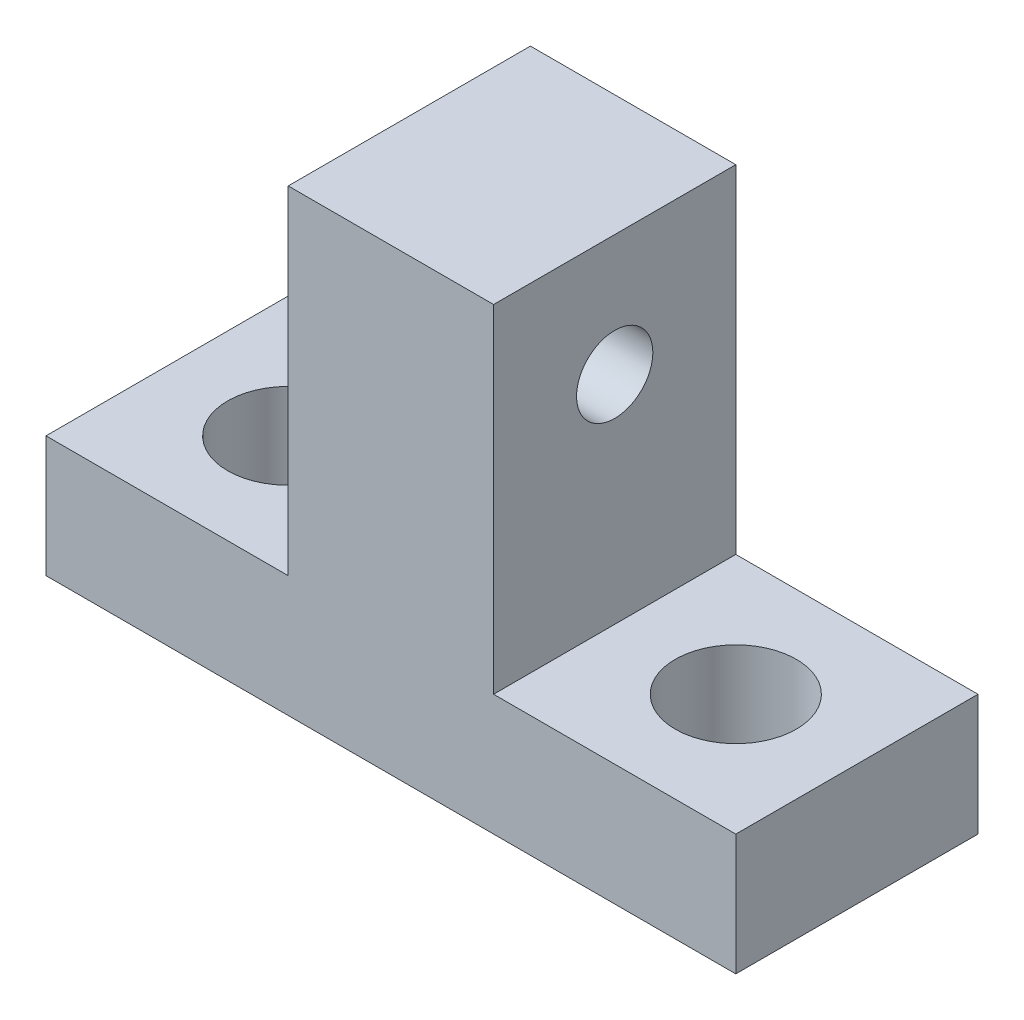
SolidWorks part; units mm, degrees
ref_plane "Front Plane" through (0, 0, 0) normal (0, 0, 1) x (1, 0, 0)
ref_plane "Top Plane" through (0, 0, 0) normal (0, 1, 0) x (1, 0, 0)
ref_plane "Right Plane" through (0, 0, 0) normal (1, 0, 0) x (0, 0, -1)
sketch "Sketch1" plane through (0, 0, 0) normal (0, 0, 1) x (1, 0, 0)
  line L1 (5.3848, 8.8495) -> (-5.3848, 8.8495)
  line L2 (5.3848, 8.8495) -> (5.3848, -8.8495)
  line L3 (5.3848, -8.8495) -> (-5.3848, -8.8495)
  line L4 (-5.3848, 8.8495) -> (-5.3848, -8.8495)
  line L5 (5.3848, 8.8495) -> (-5.3848, -8.8495) construction
  line L6 (5.3848, -8.8495) -> (-5.3848, 8.8495) construction
  line L7 (-18.0848, -8.8495) -> (18.0848, -8.8495)
  line L8 (-18.0848, -8.8495) -> (-18.0848, -15.1995)
  line L9 (-18.0848, -15.1995) -> (18.0848, -15.1995)
  line L10 (18.0848, -8.8495) -> (18.0848, -15.1995)
  point P0 (0, 0)
  point P10 (0, -15.1995)
  dimension "D1" = 6.35
  dimension "D2" = 12.7
  dimension "D3" = 10.7696
  dimension "D4" = 17.699
extrude "Boss-Extrude1" add sketch "Sketch1" along normal blind 12.7 contours L10 L7 L3 L8 L9 | L1 L4 L3 L2
sketch "Sketch2" plane through (5.3848, 0, 0) normal (1, 0, 0) x (0, 0, -1)
  line L0 (-12.7, -8.8495) -> (0, -8.8495) construction
  line L2 (-10.16, 2.4995) -> (-10.16, -8.8495)
  line L3 (-10.16, -8.8495) -> (-2.54, -8.8495)
  line L4 (-2.54, 2.4995) -> (-2.54, -8.8495)
  line L5 (-10.16, 2.4995) -> (-2.54, -8.8495) construction
  line L6 (-10.16, -8.8495) -> (-2.54, 2.4995) construction
  line L7 (-12.7, 8.8495) -> (0, 8.8495) construction
  arc A0 (-10.16, 2.4995) -> (-2.54, 2.4995) centre (-6.35, 2.4995) cw
  point P0 (-6.35, -3.175)
  point P10 (-6.35, 8.8495)
  dimension "D1" = 7.62
  dimension "D2" = 6.35
extrude "Boss-Extrude2" [suppressed] add sketch "Sketch2" along normal blind 2.54
sketch "Sketch3" [suppressed] plane through (7.62, 0, 0) normal (1, 0, 0) x (0, 0, -1)
  circle A0 centre (-6.35, 2.4995) radius 2
  arc A1 (-2.54, 2.4995) -> (-10.16, 2.4995) centre (-6.35, 2.4995) ccw construction
  dimension "D1" = 4
extrude "Cut-Extrude1" [suppressed] cut sketch "Sketch3" against normal through all
mirror "Mirror1" [suppressed] about plane through (0, 0, 0) normal (1, 0, 0)
sketch "Sketch5" plane through (5.3848, 0, 0) normal (1, 0, 0) x (0, 0, -1)
  line L0 (-12.7, 8.8495) -> (0, 8.8495) construction
  circle A0 centre (-6.35, 2.4995) radius 2
  point P5 (-6.35, 8.8495)
  dimension "D2" = 4
  dimension "D1" = 6.35
extrude "Cut-Extrude2" cut sketch "Sketch5" against normal through all
sketch "Sketch6" plane through (0, -8.8495, 0) normal (0, 1, 0) x (1, 0, 0)
  line L0 (-7.5262, 0) -> (-7.5262, -12.7) construction
  line L1 (-18.0848, 0) -> (-5.3848, 0) construction
  line L2 (-18.0848, -12.7) -> (-5.3848, -12.7) construction
  line L3 (-18.0848, -1.6786) -> (-5.3848, -1.6786) construction
  line L4 (-18.0848, -12.7) -> (-18.0848, 0) construction
  line L5 (-5.3848, -12.7) -> (-5.3848, 0) construction
  line L6 (-11.7348, -6.35) -> (11.7348, -6.35) construction
  circle A0 centre (-11.7348, -6.35) radius 3.175
  circle A1 centre (11.7348, -6.35) radius 3.175
  point P10 (-7.5262, -6.35)
  point P11 (-11.7348, -1.6786)
  point P18 (0, -6.35)
  dimension "D1" = 6.35
extrude "Cut-Extrude3" cut sketch "Sketch6" against normal through all
